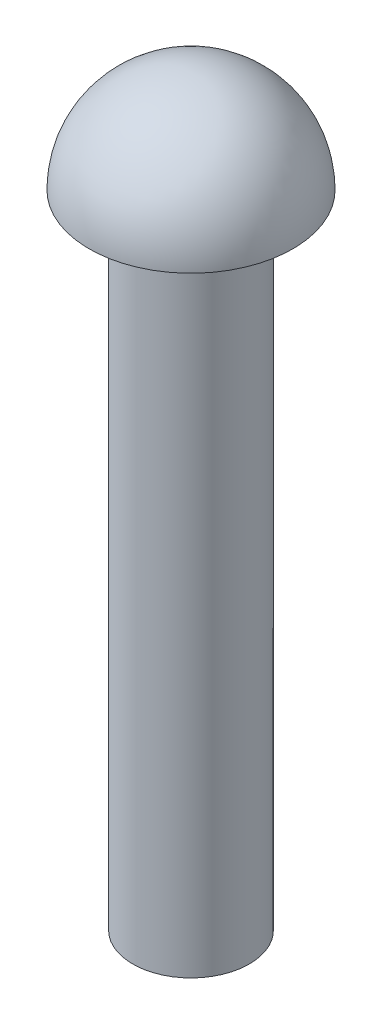
SolidWorks part; units mm, degrees
ref_plane "Front Plane" through (0, 0, 0) normal (0, 0, 1) x (1, 0, 0)
ref_plane "Top Plane" through (0, 0, 0) normal (0, 1, 0) x (1, 0, 0)
ref_plane "Right Plane" through (0, 0, 0) normal (1, 0, 0) x (0, 0, -1)
sketch "Sketch1" plane through (0, 0, 0) normal (0, 0, 1) x (1, 0, 0)
  line L0 (0, 0) -> (0, 38.2335) construction
  line L1 (0, 0) -> (3.175, 0)
  line L2 (3.175, 0) -> (3.175, 34.925)
  line L3 (3.175, 34.925) -> (5.5499, 34.925)
  arc A0 (0, 40.4749) -> (5.5499, 34.925) centre (0, 34.925) cw
  dimension "D3" = 5.5499
  dimension "D1" = 34.925
  dimension "D2" = 3.175
revolve "Revolve-Thin1" add sketch "Sketch1" angle 360 about L0 wall 2.54
